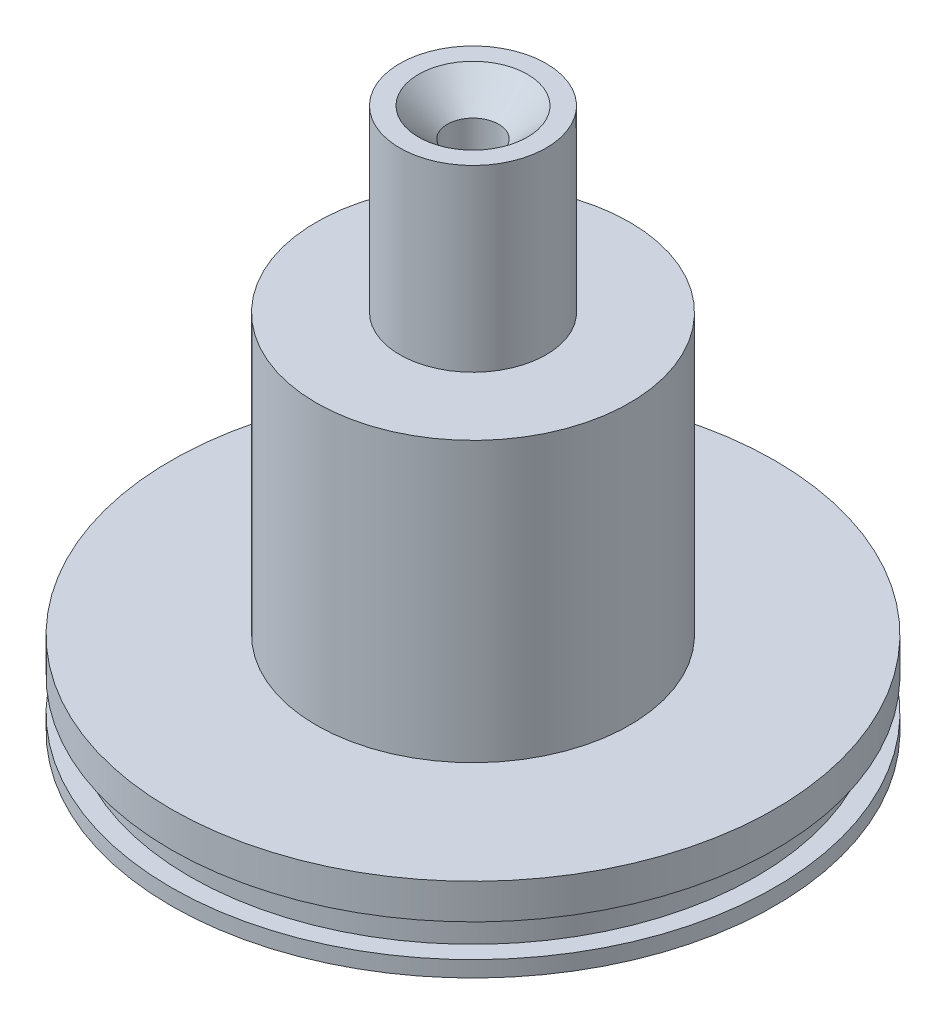
SolidWorks part; units mm, degrees
material "6061-T6 (SS)"
ref_plane "Front Plane" through (0, 0, 0) normal (0, 0, 1) x (1, 0, 0)
ref_plane "Top Plane" through (0, 0, 0) normal (0, 1, 0) x (1, 0, 0)
ref_plane "Right Plane" through (0, 0, 0) normal (1, 0, 0) x (0, 0, -1)
sketch "Sketch1" plane through (0, 0, 0) normal (0, 0, 1) x (1, 0, 0)
  line L0 (19.1516, 0) -> (19.1516, 50.8)
  line L1 (55, 0) -> (-55, 0) construction
  line L2 (19.1516, 50.8) -> (0, 50.8)
  line L3 (0, -55) -> (0, 55) construction
  line L4 (0, 50.8) -> (0, 55.0164)
  line L5 (0, 55.0164) -> (3.8862, 55.0164)
  line L6 (3.8862, 55.0164) -> (3.8862, 77.8002)
  line L7 (3.8862, 77.8002) -> (8.255, 82.169)
  line L8 (8.255, 82.169) -> (11.0998, 82.169)
  line L9 (11.0998, 82.169) -> (11.0998, 55.0164)
  line L10 (11.0998, 55.0164) -> (23.749, 55.0164)
  line L11 (23.749, 55.0164) -> (23.749, 12.7)
  line L12 (23.749, 12.7) -> (45.7708, 12.7)
  line L13 (45.7708, 12.7) -> (45.7708, 7.366)
  line L14 (45.7708, 7.366) -> (42.926, 7.366)
  line L15 (42.926, 7.366) -> (42.926, 2.413)
  line L16 (42.926, 2.413) -> (45.7708, 2.413)
  line L17 (45.7708, 2.413) -> (45.7708, 0)
  line L18 (45.7708, 0) -> (19.1516, 0)
  dimension "D1" = 19.1516
  dimension "D2" = 23.749
  dimension "D3" = 12.7
  dimension "D4" = 5.334
  dimension "D5" = 4.953
  dimension "D6" = 2.8448
  dimension "D7" = 45.7708
  dimension "D8" = 50.8
  dimension "D9" = 11.0998
  dimension "D10" = 27.1526
  dimension "D11" = 27.1526
  dimension "D12" = 3.8862
  dimension "D13" = 2.8448
  dimension "D14" = 135
  dimension "D15" = 42.3164
revolve "Revolve1" add sketch "Sketch1" angle 360 about L4
